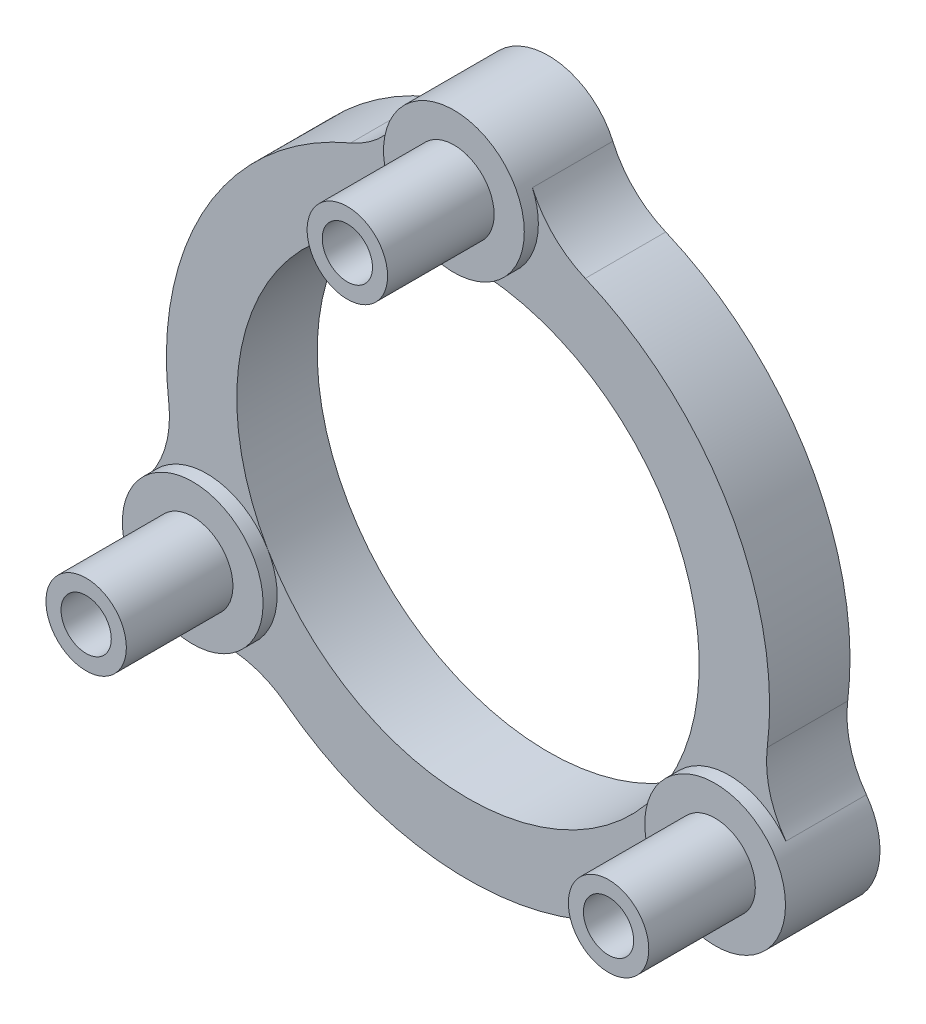
SolidWorks part; units mm, degrees
material "6061 Alloy"
ref_plane "Front" through (0, 0, 0) normal (0, 0, 1) x (1, 0, 0)
ref_plane "Top" through (0, 0, 0) normal (0, 1, 0) x (1, 0, 0)
ref_plane "Right" through (0, 0, 0) normal (1, 0, 0) x (0, 0, -1)
sketch "Sketch1" plane through (0, 0, 0) normal (0, 0, 1) x (1, 0, 0)
  circle A0 centre (0, 0) radius 11.5
  circle A4 centre (0, 0) radius 18.5
  point P11 (0, 0)
  dimension "D1" = 23
  dimension "D5" = 37
extrude "Boss-Extrude1" add sketch "Sketch1" along normal blind 4
sketch "Sketch2" plane through (0, 0, 4) normal (0, 0, 1) x (1, 0, 0)
  circle A0 centre (0, 15) radius 2
  circle A1 centre (0, 0) radius 11.5 construction
  circle A2 centre (12.9904, -7.5) radius 2
  circle A3 centre (-12.9904, -7.5) radius 2
  point P10 (0, 0)
  point P16 (0, 0)
  dimension "D1" = 4
  dimension "D2" = 15
  dimension "D3" = 3
extrude "Boss-Extrude2" add sketch "Sketch2" along normal blind 6
hole_wizard "Tap Drill for M3x0.5 Tap1" positions "3DSketch1" profile "Sketch3" hole size "M3x0.5" standard "ANSI Metric" end condition through all
sketch3d "3DSketch1"
  line L0 (0, 15, 10) -> (0, 15, 4) construction
  line L1 (12.9904, -7.5, 10) -> (12.9904, -7.5, 4) construction
  line L2 (-12.9904, -7.5, 10) -> (-12.9904, -7.5, 4) construction
  point P0 (0, 15, 10)
  point P4 (12.9904, -7.5, 10)
  point P8 (-12.9904, -7.5, 10)
sketch "Sketch3" plane through (0, 15, 10) normal (1, 0, 0) x (0, -1, 0)
  line L0 (0, 0) -> (0, 10)
  line L1 (0, 10) -> (1.25, 10)
  line L2 (1.25, 10) -> (1.25, 0)
  line L5 (1.25, 0) -> (0, 0)
  line L11 (0, -6.35) -> (0, 107.95) construction
  dimension "Thru Hole Dia." = 2.5
  dimension "Thru Hole Depth" = 10
sketch "Sketch5" plane through (0, 0, 4) normal (0, 0, 1) x (1, 0, 0)
  circle A0 centre (0, 15) radius 3.5
  circle A1 centre (12.9904, -7.5) radius 3.5
  circle A2 centre (-12.9904, -7.5) radius 3.5
  circle A3 centre (0, 0) radius 15
  circle A4 centre (0, 0) radius 24.3097
  circle M4 centre (0, 0) radius 18.5
extrude "Cut-Extrude1" cut sketch "Sketch5" against normal blind 10 contours A3 A0 A2 M4 | A3 A1 A0 M4 | A3 A2 A1 M4
fillet "Fillet1" radius 5 6 edges at (-3.4761, 14.5917, 2) (3.4761, 14.5917, 2) (14.3748, -4.2854, 2) (10.8987, -10.3062, 2) (-10.8987, -10.3062, 2) (-14.3748, -4.2854, 2)
sketch "Sketch6" plane through (0, 0, 4) normal (0, 0, 1) x (1, 0, 0)
  circle A0 centre (-12.9904, -7.5) radius 2
  circle A1 centre (-12.9904, -7.5) radius 3.5
  circle A2 centre (0, 15) radius 2
  circle A3 centre (0, 15) radius 3.5
  circle A4 centre (12.9904, -7.5) radius 2
  circle A5 centre (12.9904, -7.5) radius 3.5
  arc A6 (3.2033, 16.4103) -> (-3.2033, 16.4103) centre (0, 15) ccw construction
  circle A7 centre (0, 15) radius 2 construction
  arc A8 (-15.8134, -5.431) -> (-12.6101, -10.9793) centre (-12.9904, -7.5) ccw construction
  circle A9 centre (-12.9904, -7.5) radius 2 construction
  circle A10 centre (12.9904, -7.5) radius 2 construction
  arc A11 (12.6101, -10.9793) -> (15.8134, -5.431) centre (12.9904, -7.5) ccw construction
extrude "Boss-Extrude3" add sketch "Sketch6" along normal blind 0.7
